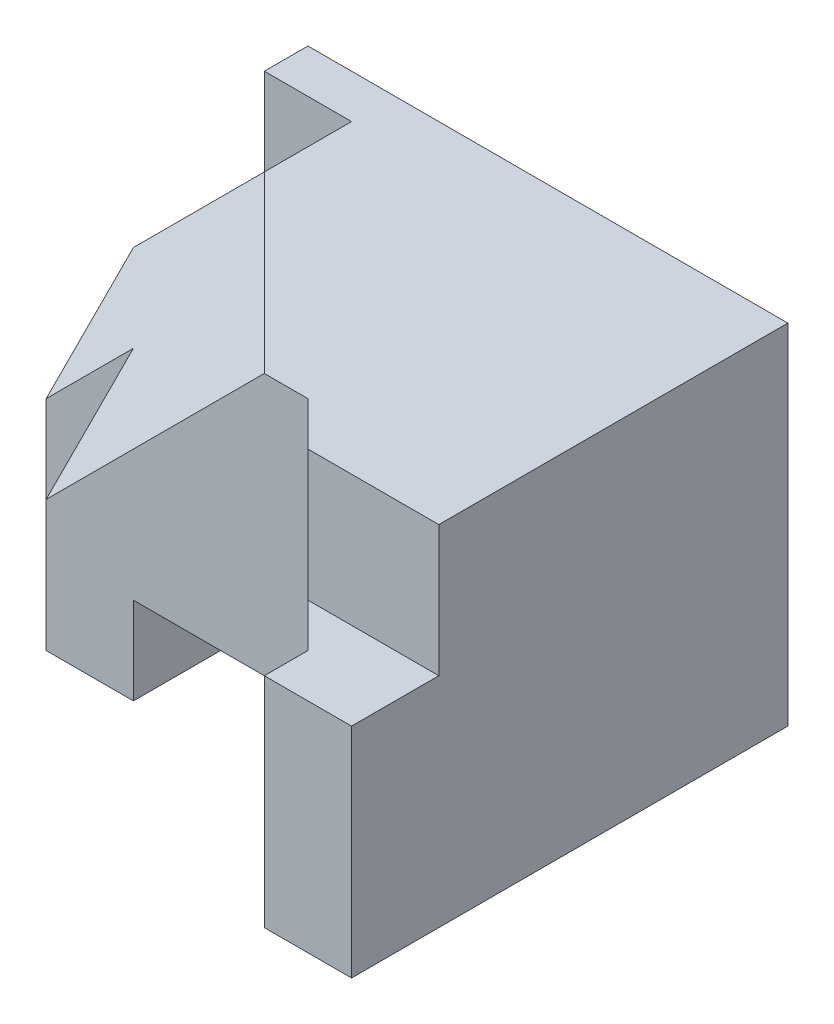
SolidWorks part; units mm, degrees
ref_plane "Front Plane" through (0, 0, 0) normal (0, 0, 1) x (1, 0, 0)
ref_plane "Top Plane" through (0, 0, 0) normal (0, 1, 0) x (1, 0, 0)
ref_plane "Right Plane" through (0, 0, 0) normal (1, 0, 0) x (0, 0, -1)
sketch "Sketch1" plane through (0, 0, 0) normal (0, 0, 1) x (1, 0, 0)
  line L1 (0, 0) -> (120, 0)
  line L2 (0, 0) -> (0, 80)
  line L3 (0, 80) -> (120, 80)
  line L4 (120, 0) -> (120, 80)
  dimension "D1" = 120
  dimension "D2" = 80
extrude "Boss-Extrude1" add sketch "Sketch1" against normal blind 100
sketch "Sketch2" plane through (0, 0, 0) normal (0, 0, 1) x (1, 0, 0)
  line L0 (0, 0) -> (120, 0) construction
  line L1 (40, 0) -> (80, 0)
  line L2 (40, 0) -> (40, 20)
  line L3 (40, 20) -> (80, 20)
  line L4 (80, 0) -> (80, 20)
  dimension "D1" = 40
  dimension "D2" = 20
  dimension "D3" = 40
extrude "Cut-Extrude1" cut sketch "Sketch2" against normal blind 100
sketch "Sketch3" plane through (0, 0, 0) normal (0, 0, 1) x (1, 0, 0)
  line L0 (0, 50) -> (10, 60)
  line L1 (0, 80) -> (0, 0) construction
  line L2 (10, 60) -> (10, 80)
  line L3 (120, 80) -> (0, 80) construction
  line L4 (10, 80) -> (0, 80)
  line L5 (0, 80) -> (0, 50)
  dimension "D1" = 10
  dimension "D2" = 30
  dimension "D3" = 20
extrude "Cut-Extrude2" cut sketch "Sketch3" against normal blind 100
sketch "Sketch4" plane through (0, 0, 0) normal (0, -1, 0) x (-1, 0, 0)
  line L1 (0, 0) -> (-20, 0)
  line L2 (0, 0) -> (0, 50)
  line L3 (0, 50) -> (-20, 50)
  line L4 (-20, 0) -> (-20, 50)
  dimension "D1" = 20
  dimension "D2" = 50
extrude "Cut-Extrude3" cut sketch "Sketch4" against normal blind 100
sketch "Sketch5" plane through (0, 0, 0) normal (0, -1, 0) x (-1, 0, 0)
  line L1 (-20, 0) -> (-80, 0)
  line L2 (-20, 0) -> (-20, 30)
  line L3 (-20, 30) -> (-80, 30)
  line L4 (-80, 0) -> (-80, 30)
  dimension "D1" = 60
  dimension "D2" = 30
extrude "Cut-Extrude4" cut sketch "Sketch5" against normal blind 100
sketch "Sketch6" plane through (0, 0, 0) normal (0, -1, 0) x (1, 0, 0)
  line L0 (80, -30) -> (100, -10)
  line L1 (80, -100) -> (80, 0) construction
  line L2 (100, -10) -> (100, 0)
  line L3 (80, 0) -> (120, 0) construction
  line L4 (100, 0) -> (80, 0)
  line L5 (80, 0) -> (80, -30)
  dimension "D1" = 10
  dimension "D2" = 20
  dimension "D3" = 20
extrude "Cut-Extrude5" cut sketch "Sketch6" against normal blind 100
sketch "Sketch7" plane through (0, 80, 0) normal (0, 1, 0) x (1, 0, 0)
  line L1 (120, 0) -> (90, 0)
  line L2 (120, 0) -> (120, 20)
  line L3 (120, 20) -> (90, 20)
  line L4 (90, 0) -> (90, 20)
  dimension "D1" = 20
  dimension "D2" = 30
extrude "Cut-Extrude6" cut sketch "Sketch7" against normal blind 30
ref_plane "Plane1" through (0, 0, -90) normal (0, 0, 1) x (1, 0, 0)
sketch "Sketch9" plane through (0, 0, -90) normal (0, 0, 1) x (1, 0, 0)
  line L0 (10, 80) -> (10, 60)
  line L1 (10, 60) -> (30, 80)
  line L2 (30, 80) -> (10, 80)
  dimension "D1" = 20
  dimension "D2" = 20
  dimension "D3" = 0
extrude "Cut-Extrude7" cut sketch "Sketch9" along normal blind 110
sketch "Sketch10" plane through (0, 80, 0) normal (0, 1, 0) x (1, 0, 0)
  line L0 (30, 30) -> (30, 90) construction
  line L1 (120, 100) -> (10, 100) construction
  point P0 (30, 70)
  dimension "D1" = 30
sketch "Sketch11" plane through (0, 0, 0) normal (-1, 0, 0) x (0, 0, 1)
  line L0 (-50, 50) -> (-50, 0) construction
  point P0 (-50, 30)
  dimension "D1" = 30
sketch "Sketch12" plane through (20, 0, 0) normal (-1, 0, 0) x (0, 0, 1)
  line L0 (-50, 70) -> (-50, 0) construction
  point P0 (-50, 50)
  dimension "D1" = 50
ref_plane "Plane2" through (6.6667, -6.6667, -6.6667) normal (-0.5774, 0.5774, 0.5774) x (0.4082, -0.4082, 0.8165)
sketch "Sketch14" plane through (0, 0, 0) normal (-1, 0, 0) x (0, 0, 1)
  line L0 (-100, 50) -> (-50, 50) construction
  point P0 (-70, 30)
  dimension "D1" = 20
  dimension "D2" = 20
ref_plane "Plane3" through (6.5789, -3.9474, -2.6316) normal (-0.8111, 0.4867, 0.3244) x (0.2782, -0.1669, 0.9459)
sketch "Sketch15" plane through (6.5789, -3.9474, -2.6316) normal (-0.8111, 0.4867, 0.3244) x (0.2782, -0.1669, 0.9459)
  line L0 (-71.2211, 84.0343) -> (-71.2211, 25.7248)
  line L1 (-71.2211, 25.7248) -> (-50.0773, 14.2915)
  line L2 (-50.0773, 14.2915) -> (-50.0773, 53.1646)
  line L3 (-50.0773, 53.1646) -> (-71.2211, 84.0343)
  line L4 (-55.6415, 42.8746) -> (-47.2953, 0) construction
extrude "Cut-Extrude8" cut sketch "Sketch15" along normal blind 110
sketch "Sketch16" plane through (0, 80, 0) normal (0, 1, 0) x (1, 0, 0)
  line L0 (80, 30) -> (30, 30) construction
  point P0 (70, 30)
  dimension "D1" = 10
sketch "Sketch17" plane through (20, 0, 0) normal (-1, 0, 0) x (0, 0, 1)
  line L0 (-30, 0) -> (-30, 70) construction
  point P0 (-30, 20)
  dimension "D1" = 20
ref_plane "Plane4" through (12.3711, -10.3093, -12.3711) normal (0.6092, -0.5077, -0.6092) x (-0.468, 0.39, -0.793)
sketch "Sketch18" plane through (12.3711, -10.3093, -12.3711) normal (0.6092, -0.5077, -0.6092) x (-0.468, 0.39, -0.793)
  line L0 (72.671, 80.6632) -> (22.2303, 106.2706)
  line L1 (22.2303, 106.2706) -> (22.2303, 28.1681)
  line L2 (22.2303, 28.1681) -> (72.671, 80.6632)
extrude "Cut-Extrude9" cut sketch "Sketch18" against normal blind 110
ref_plane "Plane5" through (11.1937, -9.3281, -7.9289) normal (-0.6748, 0.5623, 0.478) x (0.3672, -0.306, 0.8784)
sketch "Sketch19" plane through (11.1937, -9.3281, -7.9289) normal (-0.6748, 0.5623, 0.478) x (0.3672, -0.306, 0.8784)
  line L0 (-25.1273, 106.2706) -> (-70.6659, 106.2706)
  line L1 (-70.6659, 106.2706) -> (-70.6659, 23.0466)
  line L2 (-70.6659, 23.0466) -> (-25.1273, 28.1681)
  line L3 (-25.1273, 28.1681) -> (-25.1273, 106.2706)
extrude "Cut-Extrude11" cut sketch "Sketch19" along normal blind 110
sketch "Sketch20" plane through (18.3301, 24.5662, -3.0235) normal (0.5951, 0.7976, -0.0982) x (0.8036, -0.5907, 0.0727)
  line L0 (-14.6635, 46.2569) -> (-22.8093, 65.8111)
  line L1 (-22.8093, 65.8111) -> (-10.3657, 46.5717)
  line L2 (-10.3657, 46.5717) -> (-14.6635, 46.2569)
extrude "Cut-Extrude12" cut sketch "Sketch20" against normal blind 110
ref_plane "Plane6" through (0, 0, -70) normal (0, 0, 1) x (1, 0, 0)
sketch "Sketch23" plane through (0, 0, -70) normal (0, 0, 1) x (1, 0, 0)
  line L0 (0, 30) -> (0, 80)
  line L1 (0, 80) -> (41.6667, 80)
  line L2 (41.6667, 80) -> (0, 30)
  line L4 (120, 80) -> (10, 80) construction
extrude "Cut-Extrude13" cut sketch "Sketch23" along normal blind 110
ref_plane "Plane7" through (12.5279, -10.4399, -14.0938) normal (0.5812, -0.4844, -0.6539) x (-0.8137, -0.346, -0.4671)
sketch "Sketch27" plane through (0, 0, -30) normal (0, 0, 1) x (1, 0, 0)
  line L0 (70, 80) -> (20, 30)
  line L1 (30, 80) -> (0, 50) construction
  line L2 (20, 0) -> (20, 30)
  line L3 (20, 20) -> (70, 80)
  line M2 (70, 80) -> (20, 20)
extrude "Boss-Extrude4" add sketch "Sketch27" against normal blind 50 contours L2 L0 M2
ref_plane "Plane11" through (6.6667, -6.6667, -6.6667) normal (-0.5774, 0.5774, 0.5774) x (0.8165, 0.4082, 0.4082)
sketch "Sketch28" plane through (6.6667, -6.6667, -6.6667) normal (-0.5774, 0.5774, 0.5774) x (0.8165, 0.4082, 0.4082)
  line L0 (28.5774, 106.066) -> (77.5672, 77.7817)
  line L1 (77.5672, 77.7817) -> (16.3299, 42.4264)
  line L2 (16.3299, 42.4264) -> (-8.165, 84.8528)
  line L3 (-8.165, 84.8528) -> (28.5774, 106.066)
extrude "Boss-Extrude6" add sketch "Sketch28" against normal blind 40
sketch "Sketch29" plane through (0, 80, 0) normal (0, 1, 0) x (1, 0, 0)
  line L0 (30, 70) -> (41.6667, 70)
  line L1 (41.6667, 70) -> (70, 30)
  line L2 (70, 30) -> (30, 70)
extrude "Boss-Extrude7" add sketch "Sketch29" against normal blind 40
ref_plane "Plane12" through (0, 0, -50) normal (0, 0, 1) x (1, 0, 0)
sketch "Sketch30" plane through (0, 0, -50) normal (0, 0, 1) x (1, 0, 0)
  line L0 (0, 0) -> (0, 30)
  line L1 (0, 30) -> (20, 50)
  line L2 (20, 50) -> (20, 0)
  line L3 (20, 0) -> (0, 0)
  line L4 (0, 0) -> (20, 0)
  dimension "D1" = 30
  dimension "D2" = 20
  dimension "D3" = 20
  dimension "D4" = 20
extrude "Cut-Extrude18" cut sketch "Sketch30" against normal blind 20 and the other way blind 84 contours L4 L0 L1 L2
sketch "Sketch33" plane through (11.1937, -9.3281, -7.9289) normal (-0.6748, 0.5623, 0.478) x (0.3672, -0.306, 0.8784)
  line L0 (-70.6659, 37.2471) -> (-67.9872, 37.1307)
  line L1 (-67.9872, 37.1307) -> (-70.6659, 23.0466) construction
  line L2 (-70.6659, 37.2471) -> (-67.9872, 37.1307) construction
  line L3 (-67.9872, 37.1307) -> (-70.6659, 23.0466)
  line L4 (-70.6659, 23.0466) -> (-70.6659, 37.2471)
extrude "Cut-Extrude19" cut sketch "Sketch33" against normal blind 20
sketch "Sketch34" plane through (0, 0, -100) normal (0, 0, -1) x (-1, 0, 0)
  line L1 (0, 50) -> (-40, 50)
  line L2 (0, 50) -> (0, 0)
  line L3 (0, 0) -> (-40, 0)
  line L4 (-40, 50) -> (-40, 0)
extrude "Boss-Extrude8" add sketch "Sketch34" against normal blind 30
sketch "Sketch35" plane through (-15, 15, 0) normal (0.7071, -0.7071, 0) x (0, 0, -1)
  line L1 (50, 35.3553) -> (70, 35.3553)
  line L2 (50, 35.3553) -> (50, 49.4975)
  line L3 (50, 49.4975) -> (70, 49.4975)
  line L4 (70, 35.3553) -> (70, 49.4975)
extrude "Cut-Extrude20" cut sketch "Sketch35" against normal blind 30
sketch "Sketch36" plane through (0, 0, 0) normal (-1, 0, 0) x (0, 0, 1)
  line L0 (-100, 0) -> (-70, 0) construction
  line L1 (-70, 0) -> (-50, 0)
  line L2 (-70, 0) -> (-70, 30)
  line L3 (-70, 30) -> (-50, 30)
  line L4 (-50, 0) -> (-50, 30)
  line L5 (-70, 50) -> (-70, 0) construction
  dimension "D1" = 20
  dimension "D2" = 30
extrude "Boss-Extrude9" add sketch "Sketch36" against normal blind 30
sketch "Sketch37" plane through (0, 0, -50) normal (0, 0, 1) x (1, 0, 0)
  line L0 (0, 30) -> (20, 50)
  line L1 (20, 50) -> (20, 30)
  line L2 (20, 30) -> (0, 30)
extrude "Boss-Extrude10" add sketch "Sketch37" against normal blind 30
ref_plane "Plane13" through (6.6667, -6.6667, -6.6667) normal (-0.5774, 0.5774, 0.5774) x (0.8165, 0.4082, 0.4082)
sketch "Sketch38" plane through (6.6667, -6.6667, -6.6667) normal (-0.5774, 0.5774, 0.5774) x (0.8165, 0.4082, 0.4082)
  line L0 (4.0825, 91.9239) -> (-8.165, 56.5685)
  line L1 (-8.165, 56.5685) -> (16.3299, 70.7107)
  line L2 (16.3299, 70.7107) -> (4.0825, 91.9239)
extrude "Boss-Extrude11" add sketch "Sketch38" against normal blind 30
ref_plane "Plane14" through (6.6667, -6.6667, -6.6667) normal (-0.5774, 0.5774, 0.5774) x (0.8165, 0.4082, 0.4082)
sketch "Sketch39" plane through (6.6667, -6.6667, -6.6667) normal (-0.5774, 0.5774, 0.5774) x (0.8165, 0.4082, 0.4082)
  line L0 (-8.165, 84.8528) -> (4.0825, 91.9239)
  line L1 (4.0825, 91.9239) -> (-8.165, 56.5685)
  line L2 (-8.165, 56.5685) -> (-8.165, 84.8528)
extrude "Boss-Extrude12" add sketch "Sketch39" against normal blind 30
sketch "Sketch40" plane through (0, 0, 0) normal (-1, 0, 0) x (0, 0, 1)
  line L0 (-70, 30) -> (-70, 50)
  line L1 (-70, 50) -> (-50, 30)
  line L2 (-50, 30) -> (-70, 30)
extrude "Boss-Extrude13" add sketch "Sketch40" against normal blind 30
sketch "Sketch41" plane through (0, 0, -30) normal (0, 0, 1) x (1, 0, 0)
  line L1 (40, 20) -> (80, 20)
  line L2 (40, 20) -> (40, 0)
  line L3 (40, 0) -> (80, 0)
  line L4 (80, 20) -> (80, 0)
extrude "Cut-Extrude21" cut sketch "Sketch41" against normal blind 172
